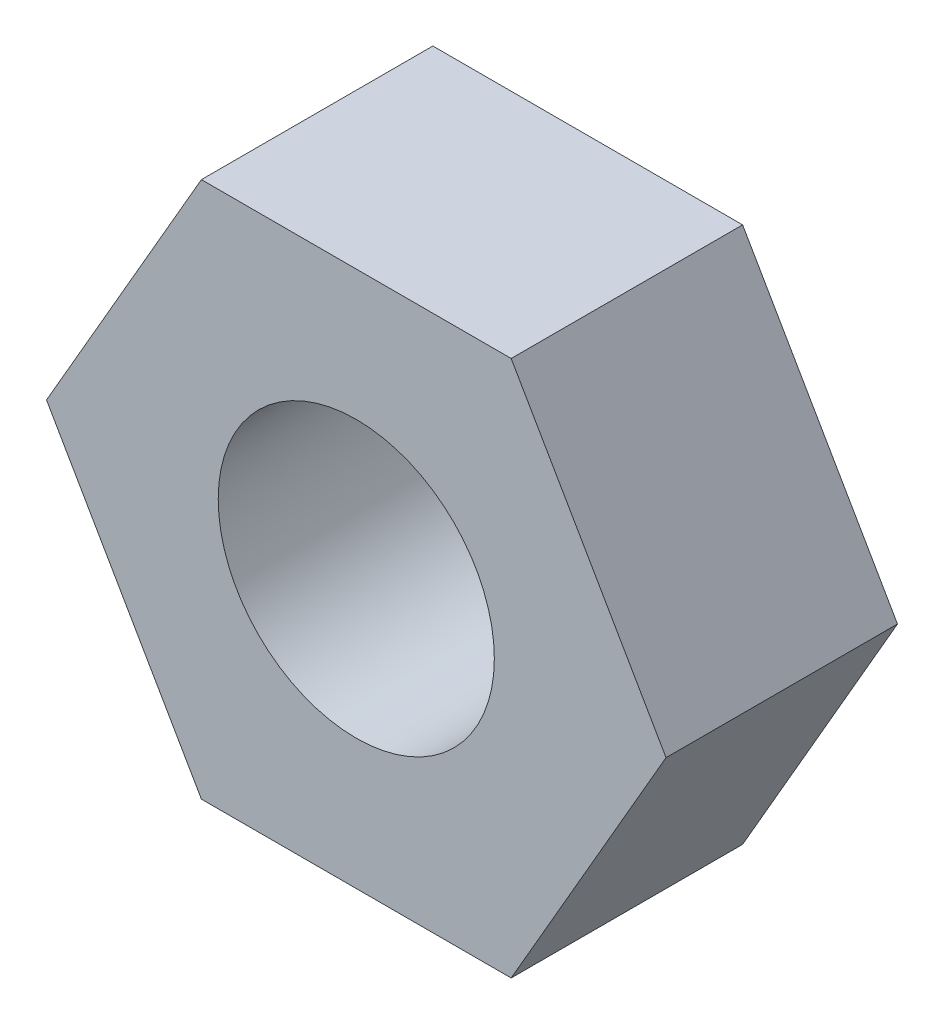
SolidWorks part; units mm, degrees
ref_plane "Front Plane" through (0, 0, 0) normal (0, 0, 1) x (1, 0, 0)
ref_plane "Top Plane" through (0, 0, 0) normal (0, 1, 0) x (1, 0, 0)
ref_plane "Right Plane" through (0, 0, 0) normal (1, 0, 0) x (0, 0, -1)
sketch "Sketch1" plane through (0, 0, 0) normal (0, 0, 1) x (1, 0, 0)
  line L0 (55, 0) -> (-55, 0) construction
  line L1 (2.2437, 0) -> (1.1218, 1.9431)
  line L2 (1.1218, 1.9431) -> (-1.1218, 1.9431)
  line L3 (-1.1218, 1.9431) -> (-2.2437, 0)
  line L4 (-2.2437, 0) -> (-1.1218, -1.9431)
  line L5 (-1.1218, -1.9431) -> (1.1218, -1.9431)
  line L6 (1.1218, -1.9431) -> (2.2437, 0)
  circle A0 centre (0, 0) radius 1.9431 construction
  circle A1 centre (0, 0) radius 1
  dimension "D2" = 2
  dimension "D1" = 3.8862
extrude "Boss-Extrude1" add sketch "Sketch1" along normal blind 1.6764
